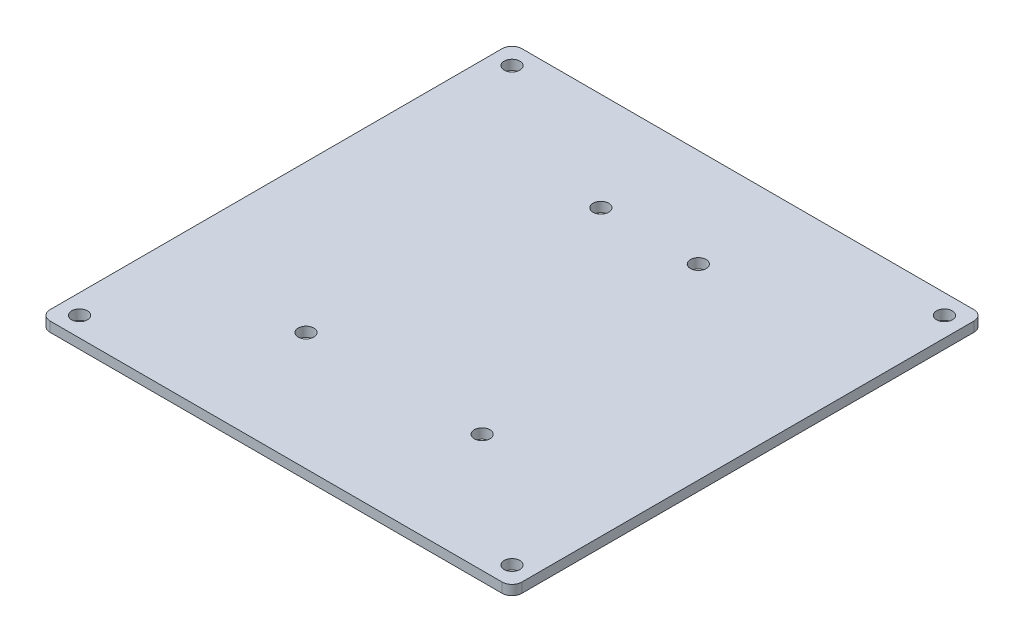
SolidWorks part; units mm, degrees
ref_plane "Front Plane" through (0, 0, 0) normal (0, 0, 1) x (1, 0, 0)
ref_plane "Top Plane" through (0, 0, 0) normal (0, 1, 0) x (1, 0, 0)
ref_plane "Right Plane" through (0, 0, 0) normal (1, 0, 0) x (0, 0, -1)
sketch "Sketch2" plane through (0, 0, 0) normal (0, 1, 0) x (1, 0, 0)
  line L0 (0, 152.4) -> (0, -152.4) construction
  line L1 (-152.4, -152.4) -> (152.4, -152.4)
  line L2 (-152.4, -152.4) -> (-152.4, 152.4)
  line L3 (-152.4, 152.4) -> (152.4, 152.4)
  line L4 (152.4, -152.4) -> (152.4, 152.4)
  line L5 (-152.4, -152.4) -> (152.4, 152.4) construction
  line L6 (-152.4, 152.4) -> (152.4, -152.4) construction
  line L7 (-152.4, 0) -> (152.4, 0) construction
  line L8 (0, 0) -> (0, -76.2) construction
  line L9 (0, -76.2) -> (56.896, -76.2) construction
  line L10 (0, -76.2) -> (-56.896, -76.2) construction
  line L11 (0, 0) -> (0, 88.9) construction
  line L12 (0, 88.9) -> (31.496, 88.9) construction
  line L13 (0, 88.9) -> (-31.496, 88.9) construction
  line L15 (152.4, 152.4) -> (142.494, 152.4)
  line L16 (152.4, 152.4) -> (152.4, 142.494)
  line L19 (152.4, 152.4) -> (139.7, 139.7) construction
  line L20 (152.4, 142.494) -> (142.494, 152.4) construction
  circle A0 centre (56.896, -76.2) radius 5.08
  circle A1 centre (-56.896, -76.2) radius 5.08
  circle A2 centre (31.496, 88.9) radius 5.08
  circle A3 centre (-31.496, 88.9) radius 5.08
  circle A4 centre (139.7, 139.7) radius 5.08
  circle A5 centre (-139.7, 139.7) radius 5.08
  circle A6 centre (139.7, -139.7) radius 5.08
  circle A7 centre (-139.7, -139.7) radius 5.08
  point P0 (0, 0)
  point P24 (147.447, 147.447)
  dimension "D3" = 76.2
  dimension "D6" = 10.16
  dimension "D7" = 10.16
  dimension "D9" = 12.7
  dimension "D1" = 304.8
  dimension "D2" = 304.8
  dimension "D4" = 113.792
  dimension "D5" = 31.496
  dimension "D8" = 12.7
  dimension "D10" = 88.9
extrude "Boss-Extrude1" add sketch "Sketch2" along normal blind 6.35
fillet "Fillet1" radius 6.35 1 edges at (-152.4, 3.175, 152.4)
fillet "Fillet2" radius 6.35 3 edges at (152.4, 3.175, 152.4) (152.4, 3.175, -152.4) (-152.4, 3.175, -152.4)
sketch "Sketch3" plane through (0, 6.35, 0) normal (0, 1, 0) x (1, 0, 0)
  line L0 (-152.4, 0) -> (152.4, 0) construction
  line L1 (-152.4, -146.05) -> (-152.4, 146.05) construction
  line L2 (152.4, -146.05) -> (152.4, 146.05) construction
  line L3 (0, 152.4) -> (0, -152.4) construction
  line L4 (-146.05, 152.4) -> (146.05, 152.4) construction
  line L5 (-146.05, -152.4) -> (146.05, -152.4) construction
